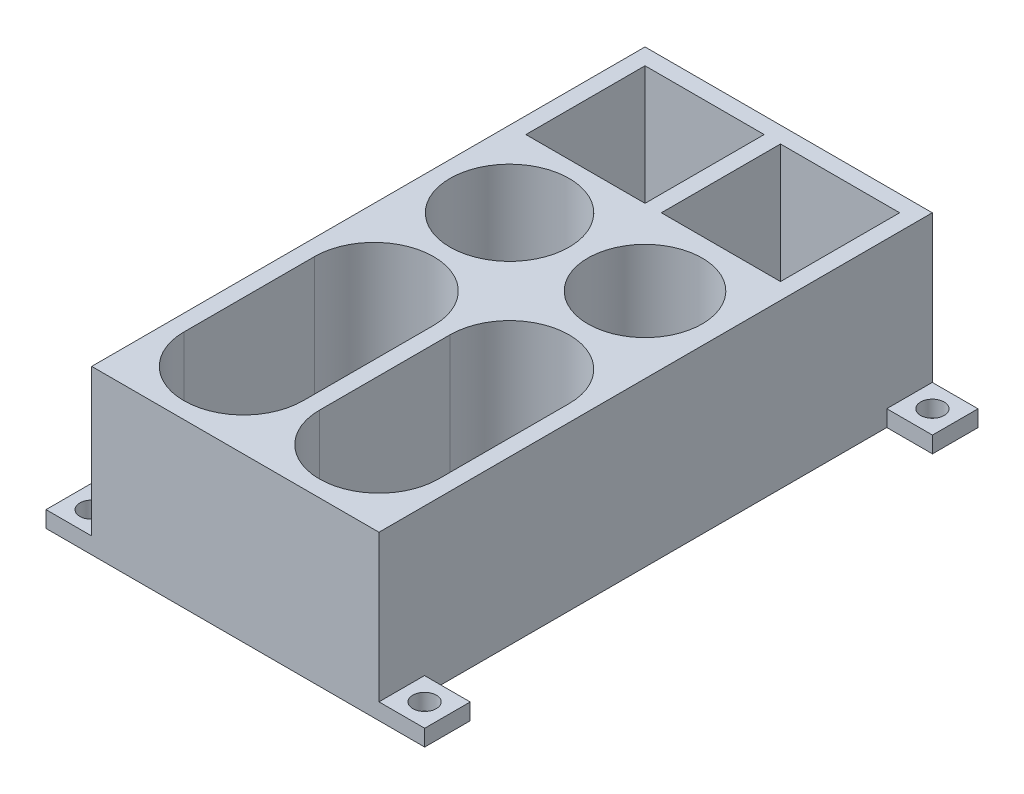
SolidWorks part; units mm, degrees
ref_plane "Ebene vorne" through (0, 0, 0) normal (0, 0, 1) x (1, 0, 0)
ref_plane "Ebene oben" through (0, 0, 0) normal (0, 1, 0) x (1, 0, 0)
ref_plane "Ebene rechts" through (0, 0, 0) normal (1, 0, 0) x (0, 0, -1)
sketch "Skizze1" plane through (0, 0, 0) normal (0, 1, 0) x (1, 0, 0)
  line L0 (-10.375, -10.75) -> (-10.375, -30.75) construction
  line L1 (-22, 42.375) -> (22, 42.375)
  line L2 (-22, 42.375) -> (-22, -42.375)
  line L3 (-22, -42.375) -> (22, -42.375)
  line L4 (22, 42.375) -> (22, -42.375)
  line L5 (-19.5, 39.875) -> (-1.25, 39.875)
  line L6 (-19.5, 39.875) -> (-19.5, 21.625)
  line L7 (-19.5, 21.625) -> (-1.25, 21.625)
  line L8 (-1.25, 39.875) -> (-1.25, 21.625)
  line L9 (1.25, 39.875) -> (19.5, 39.875)
  line L10 (1.25, 39.875) -> (1.25, 21.625)
  line L11 (1.25, 21.625) -> (19.5, 21.625)
  line L12 (19.5, 39.875) -> (19.5, 21.625)
  line L13 (-1.25, -10.75) -> (-1.25, -30.75)
  line L14 (-19.5, -10.75) -> (-19.5, -30.75)
  line L15 (10.375, -10.75) -> (10.375, -30.75) construction
  line L16 (19.5, -10.75) -> (19.5, -30.75)
  line L17 (1.25, -10.75) -> (1.25, -30.75)
  circle A0 centre (-10.375, 10) radius 9.125
  circle A1 centre (10.375, 10) radius 8.7538
  arc A2 (-1.25, -10.75) -> (-19.5, -10.75) centre (-10.375, -10.75) ccw
  arc A3 (-19.5, -30.75) -> (-1.25, -30.75) centre (-10.375, -30.75) ccw
  arc A4 (19.5, -10.75) -> (1.25, -10.75) centre (10.375, -10.75) ccw
  arc A5 (1.25, -30.75) -> (19.5, -30.75) centre (10.375, -30.75) ccw
  point P4 (0, 42.375)
  point P6 (22, 0)
  point P21 (-10.375, -20.75)
  point P31 (10.375, -20.75)
  dimension "D11" = 18.25
  dimension "D2" = 84.75
  dimension "D3" = 18.25
  dimension "D4" = 18.25
  dimension "D5" = 2.5
  dimension "D6" = 2.5
  dimension "D7" = 18.25
  dimension "D8" = 18.25
  dimension "D9" = 20
  dimension "D10" = 18.25
  dimension "D12" = 11.625
  dimension "D13" = 11.625
  dimension "D14" = 2.5
  dimension "D15" = 11.625
  dimension "D16" = 11.625
  dimension "D17" = 2.5
  dimension "D18" = 44
extrude "Aufsatz-Linear austragen1" add sketch "Skizze1" along normal blind 25
sketch "Skizze2" plane through (0, 0, 0) normal (0, -1, 0) x (1, 0, 0)
  line L1 (-22, 42.375) -> (-29, 42.375)
  line L2 (-22, 42.375) -> (-22, 35.4014)
  line L3 (-22, 35.4014) -> (-29, 35.4014)
  line L4 (-29, 42.375) -> (-29, 35.4014)
  circle A0 centre (-25.5, 38.8882) radius 1.8
  point P10 (-25.5, 42.375)
  point P12 (-29, 38.8882)
extrude "Aufsatz-Linear austragen2" add sketch "Skizze2" against normal blind 2.5
mirror "Spiegeln1" about plane through (0, 0, 0) normal (1, 0, 0) of "Aufsatz-Linear austragen2"
mirror "Spiegeln2" about plane through (0, 0, 0) normal (0, 0, 1) of "Spiegeln1", "Aufsatz-Linear austragen2"
